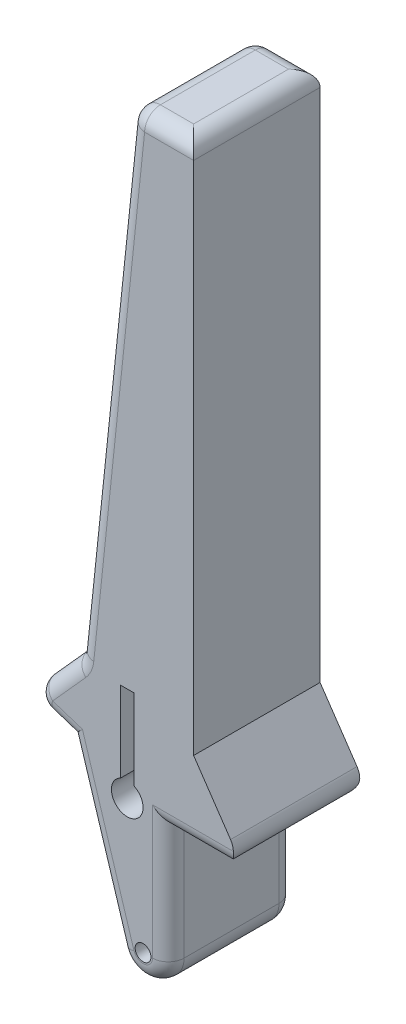
SolidWorks part; units mm, degrees
material "Polyurethane Foam Rigid"
ref_plane "Front" through (0, 0, 0) normal (0, 0, 1) x (1, 0, 0)
ref_plane "Top" through (0, 0, 0) normal (0, 1, 0) x (1, 0, 0)
ref_plane "Right" through (0, 0, 0) normal (1, 0, 0) x (0, 0, -1)
sketch "Sketch1" plane through (0, 0, 0) normal (0, 0, 1) x (1, 0, 0)
  line L2 (16, 62) -> (16, 230)
  line L3 (16, 230) -> (-4, 230)
  line L5 (-4, 230) -> (-20.7246, 70.8765)
  line L6 (-23.1681, 47.6273) -> (-7.64, -2.3727)
  line L7 (-20.7246, 70.8765) -> (-37.4294, 52.2768)
  line L8 (-37.4294, 52.2768) -> (-23.1681, 47.6273)
  line L9 (16, 62) -> (33, 37)
  line L10 (33, 37) -> (8, 37)
  line L11 (8, 0) -> (8, 37)
  line L12 (-5, 39.7203) -> (-5, 69.7203) construction
  line L13 (-2.875, 69.7203) -> (-7.125, 69.7203)
  line L14 (-2.875, 69.7203) -> (-2.875, 44.2463)
  line L15 (-7.125, 69.7203) -> (-7.125, 44.2463)
  circle A0 centre (0, 0) radius 2.5
  arc A1 (8, 0) -> (-7.64, -2.3727) centre (0, 0) cw
  arc A3 (-2.875, 44.2463) -> (-7.125, 44.2463) centre (-5, 39.7203) cw
  point P19 (-5, 69.7203)
  dimension "D1" = 5
  dimension "D2" = 8
  dimension "D8" = 39.7203
  dimension "D7" = 5
  dimension "D3" = 168
  dimension "D4" = 230
  dimension "D5" = 20
  dimension "D6" = 50
  dimension "D9" = 37
  dimension "D10" = 5
  dimension "D11" = 25
  dimension "D12" = 25
  dimension "D13" = 15
  dimension "D14" = 6
  dimension "D15" = 25
  dimension "D16" = 8
  dimension "D17" = 0
  dimension "D18" = 160
  dimension "D19" = 30
  dimension "D20" = 4.25
extrude "Boss-Extrude1" add sketch "Sketch1" along normal blind 40
fillet "Fillet1" radius 5 21 edges at (1.1999, -7.9095, 0) (1.1999, -7.9095, 40) (6, 230, 40) (6, 230, 0) (-15.4041, 22.6273, 40) (-15.4041, 22.6273, 0) (16, 230, 20) (-4, 230, 20) (-12.3623, 150.4382, 40) (-12.3623, 150.4382, 0) (-30.2988, 49.952, 40) (-29.077, 61.5766, 40) (-30.2988, 49.952, 0) (-29.077, 61.5766, 0) (-20.7246, 70.8765, 20) (-37.4294, 52.2768, 20) (8, 18.5, 40) (8, 18.5, 0) (33, 37, 20) (20.5, 37, 0) (20.5, 37, 40)
ref_plane "Plane1" through (0, 0, 20) normal (0, 0, 1) x (1, 0, 0)
